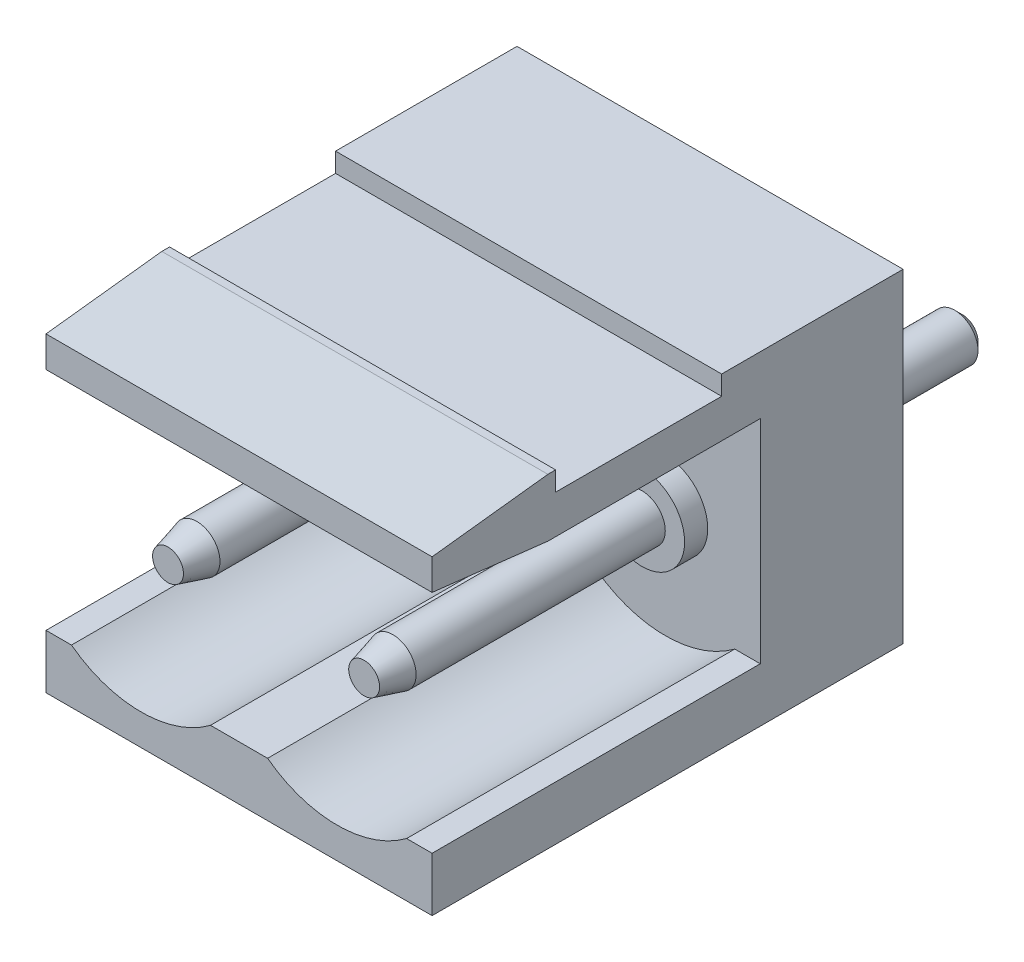
SolidWorks part; units mm, degrees
ref_plane "Plan de face" through (0, 0, 0) normal (0, 0, 1) x (1, 0, 0)
ref_plane "Plan de dessus" through (0, 0, 0) normal (0, 1, 0) x (1, 0, 0)
ref_plane "Plan de droite" through (0, 0, 0) normal (1, 0, 0) x (0, 0, -1)
sketch "Esquisse1" plane through (0, 0, 0) normal (0, 0, 1) x (1, 0, 0)
  line L1 (0, 0) -> (10, 0)
  line L2 (0, 0) -> (0, 8.4)
  line L3 (0, 8.4) -> (10, 8.4)
  line L4 (10, 0) -> (10, 8.4)
  dimension "D1" = 10
  dimension "D2" = 8.4
extrude "Boss.-Extru.1" add sketch "Esquisse1" along normal blind 12.2
sketch "Esquisse2" plane through (0, 0, 12.2) normal (0, 0, 1) x (1, 0, 0)
  line L0 (0, 8.4) -> (0, 0) construction
  line L2 (0, 1.4) -> (0, 6.9)
  line L3 (0, 6.9) -> (10, 6.9)
  line L4 (10, 1.4) -> (10, 6.9)
  line L5 (10, 0) -> (10, 8.4) construction
  line L6 (0, 1.4) -> (0.66, 1.4)
  line L7 (4.26, 1.4) -> (5.74, 1.4)
  line L8 (9.34, 1.4) -> (10, 1.4)
  line L9 (2.46, 3.8) -> (7.54, 3.8) construction
  line L10 (0, 0) -> (10, 0) construction
  line L11 (10, 8.4) -> (0, 8.4) construction
  arc A0 (0.66, 1.4) -> (4.26, 1.4) centre (2.46, 3.8) ccw
  arc A1 (5.74, 1.4) -> (9.34, 1.4) centre (7.54, 3.8) ccw
  dimension "D2" = 3
  dimension "D1" = 5.08
  dimension "D3" = 3.8
  dimension "D4" = 1.4
  dimension "D5" = 1.5
extrude "Enlèv. mat.-Extru.1" cut sketch "Esquisse2" against normal blind 8.5
sketch "Esquisse3" plane through (0, 0, 0) normal (-1, 0, 0) x (0, 0, 1)
  line L0 (12.2, 8.4) -> (0, 8.4) construction
  line L1 (4.7, 8.4) -> (9, 8.4)
  line L2 (4.7, 8.4) -> (4.7, 7.9)
  line L3 (4.7, 7.9) -> (9, 7.9)
  line L4 (9, 8.4) -> (9, 7.9)
  line L5 (12.2, 8.4) -> (12.2, 6.9) construction
  line L6 (12.2, 8.4) -> (9.2, 8.4)
  line L7 (9.2, 8.4) -> (12.2, 8.05)
  line L8 (12.2, 8.05) -> (12.2, 8.4)
  line L9 (12.2, 7.25) -> (12.2, 6.9)
  line L10 (12.2, 6.9) -> (9.2, 6.9)
  line L11 (3.7, 6.9) -> (12.2, 6.9) construction
  line L12 (9.2, 6.9) -> (12.2, 7.25)
  dimension "D1" = 0.5
  dimension "D2" = 4.3
  dimension "D3" = 3.2
  dimension "D4" = 3
  dimension "D5" = 0.8
extrude "Enlèv. mat.-Extru.2" cut sketch "Esquisse3" against normal through all
sketch "Esquisse4" plane through (0, 0, 0) normal (0, 0, -1) x (-1, 0, 0)
  line L0 (-10, 3.75) -> (-7.54, 3.75) construction
  line L1 (-10, 0) -> (-10, 8.4) construction
  line L2 (-7.54, 3.75) -> (-2.46, 3.75) construction
  line L3 (-2.46, 3.75) -> (0, 3.75) construction
  line L4 (0, 8.4) -> (0, 0) construction
  line L5 (0, 0) -> (-10, 0) construction
  circle A0 centre (-7.54, 3.75) radius 0.6
  circle A1 centre (-2.46, 3.75) radius 0.6
  dimension "D2" = 1.2
  dimension "D1" = 5.08
  dimension "D3" = 3.75
extrude "Boss.-Extru.2" add sketch "Esquisse4" along normal blind 4 and the other way blind 11.5
chamfer "Chanfrein1" distance 0.2 angle 75 2 edges at (6.94, 3.75, 11.5) (1.86, 3.75, 11.5)
chamfer "Chanfrein2" distance 0.2 angle 45 2 edges at (6.94, 3.75, -4) (1.86, 3.75, -4)
sketch "Esquisse5" plane through (0, 0, 3.7) normal (0, 0, 1) x (1, 0, 0)
  circle A0 centre (2.46, 3.75) radius 1.1
  circle A1 centre (7.54, 3.75) radius 1.1
  dimension "D1" = 2.2
extrude "Boss.-Extru.3" add sketch "Esquisse5" along normal blind 0.6
